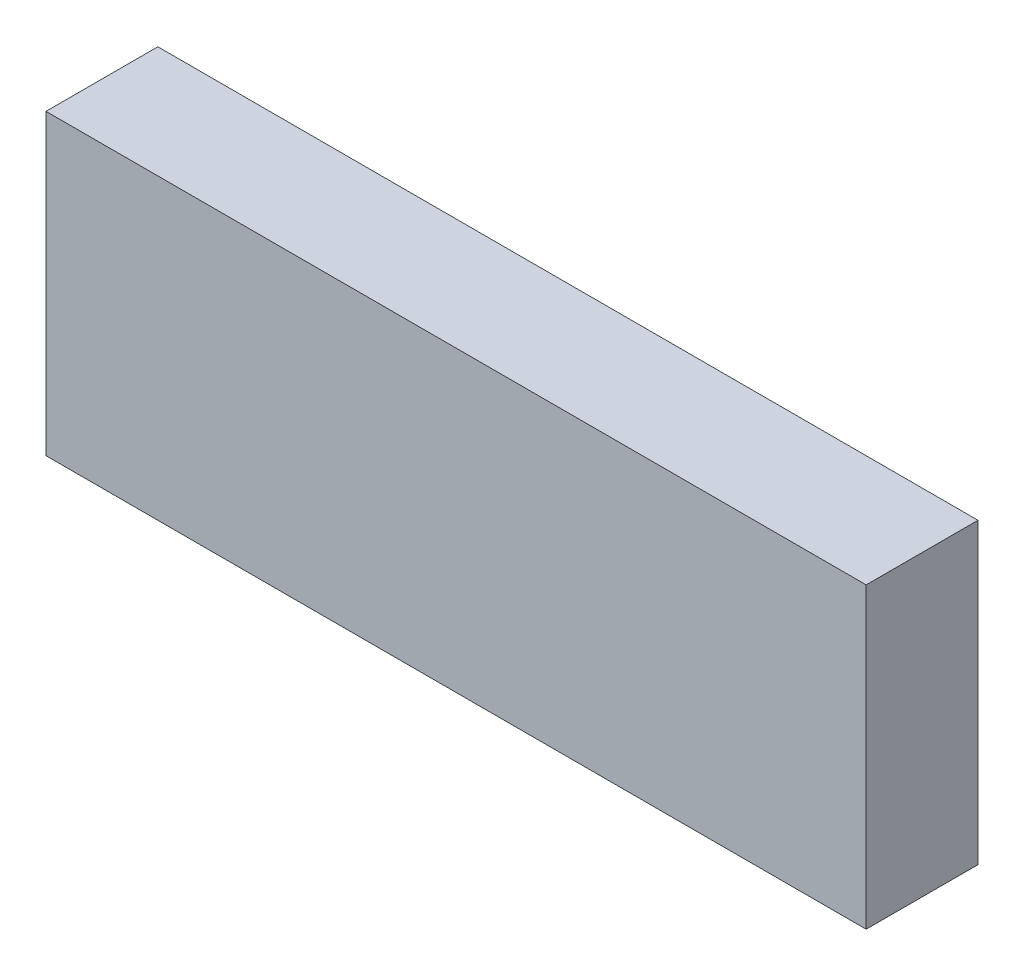
SolidWorks part; units mm, degrees
ref_plane "Front Plane" through (0, 0, 0) normal (0, 0, 1) x (1, 0, 0)
ref_plane "Top Plane" through (0, 0, 0) normal (0, 1, 0) x (1, 0, 0)
ref_plane "Right Plane" through (0, 0, 0) normal (1, 0, 0) x (0, 0, -1)
sketch "Sketch1" plane through (0, 0, 0) normal (0, 0, 1) x (1, 0, 0)
  line L1 (-7, -0.5) -> (15, -0.5)
  line L2 (-7, -0.5) -> (-7, 7.5)
  line L3 (-7, 7.5) -> (15, 7.5)
  line L4 (15, -0.5) -> (15, 7.5)
  point P0 (0, 0)
  dimension "D1" = 8
  dimension "D2" = 22
extrude "Boss-Extrude1" add sketch "Sketch1" along normal blind 3
